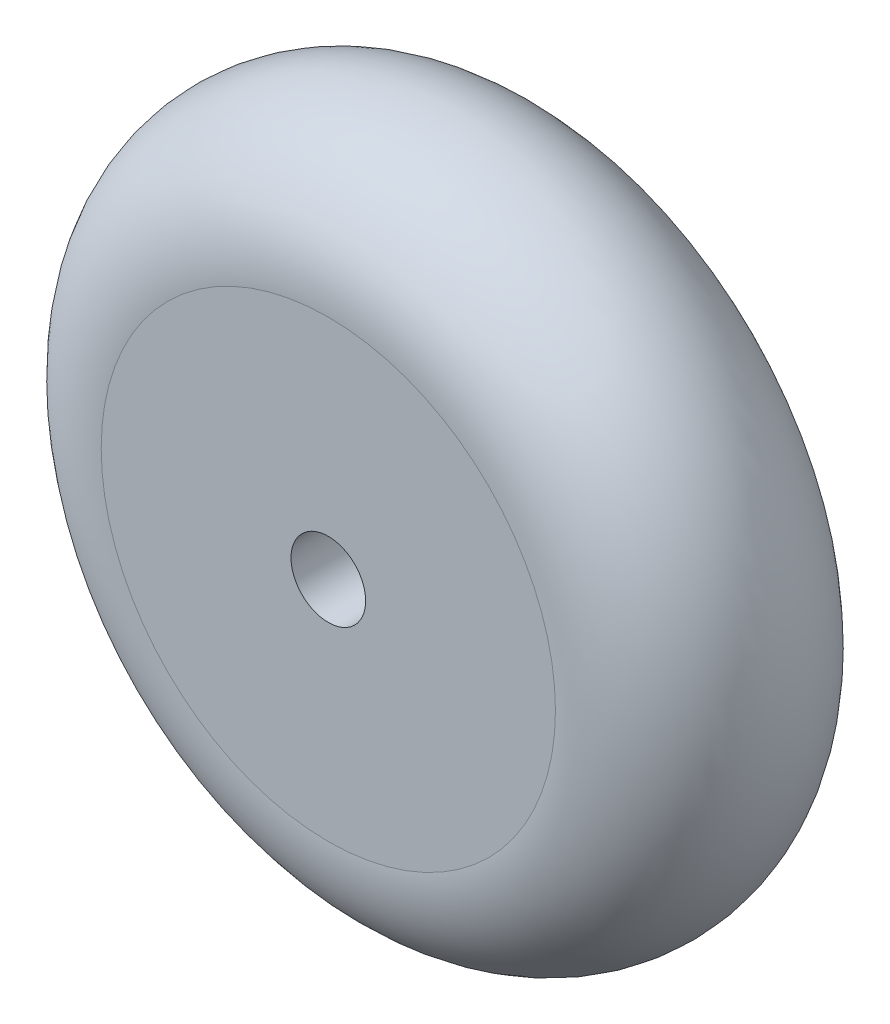
SolidWorks part; units mm, degrees
ref_plane "Front Plane" through (0, 0, 0) normal (0, 0, 1) x (1, 0, 0)
ref_plane "Top Plane" through (0, 0, 0) normal (0, 1, 0) x (1, 0, 0)
ref_plane "Right Plane" through (0, 0, 0) normal (1, 0, 0) x (0, 0, -1)
sketch "Sketch1" plane through (0, 0, 0) normal (0, 1, 0) x (1, 0, 0)
  line L0 (0, 0) -> (0, 25)
  line L1 (0, 25) -> (-24.3446, 25)
  line L2 (-24.3446, 0) -> (0, 0)
  arc A0 (-24.3446, 25) -> (-24.3446, 0) centre (-25, 12.5) ccw
  dimension "D1" = 25
  dimension "D3" = 25
revolve "Revolve1" add sketch "Sketch1" angle 360 about L0
sketch "Sketch2" plane through (0, 0, -25) normal (0, 0, -1) x (-1, 0, 0)
  circle A0 centre (0, 0) radius 4
  dimension "D1" = 8
extrude "Cut-Extrude1" cut sketch "Sketch2" against normal through all
